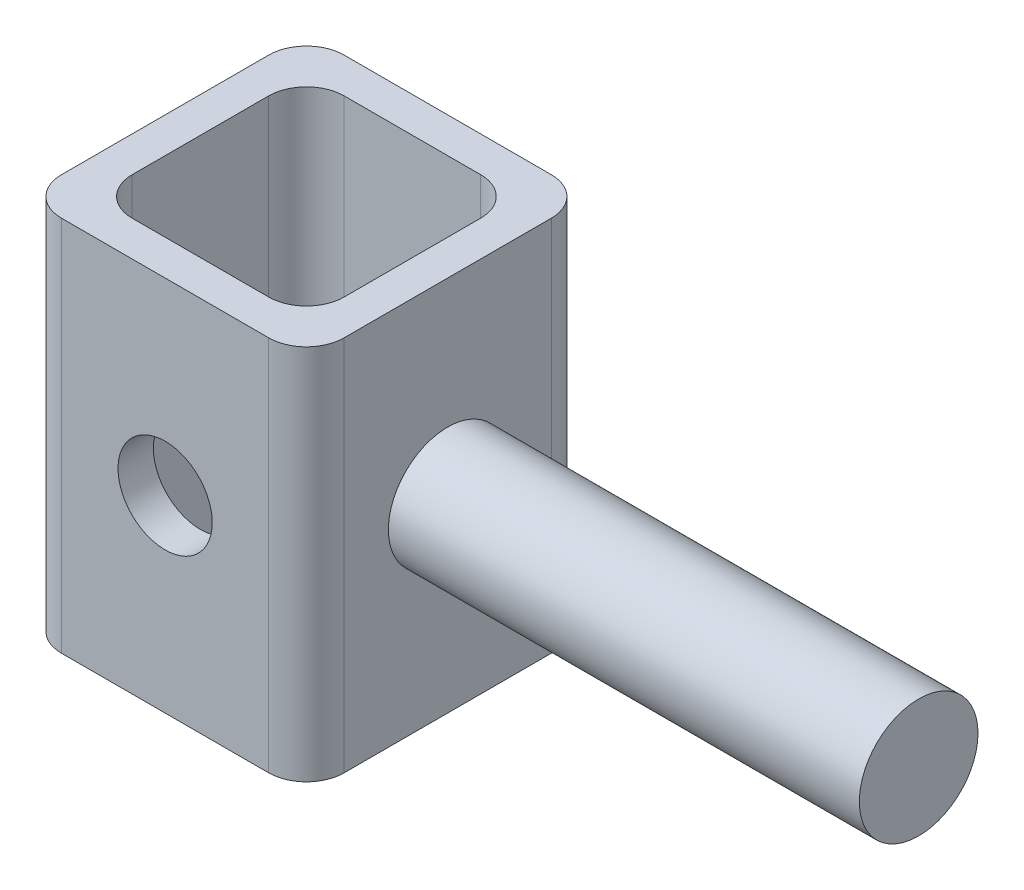
SolidWorks part; units mm, degrees
ref_plane "Front Plane" through (0, 0, 0) normal (0, 0, 1) x (1, 0, 0)
ref_plane "Top Plane" through (0, 0, 0) normal (0, 1, 0) x (1, 0, 0)
ref_plane "Right Plane" through (0, 0, 0) normal (1, 0, 0) x (0, 0, -1)
sketch "Sketch1" plane through (0, 0, 0) normal (0, 1, 0) x (1, 0, 0)
  line L1 (0, 0) -> (19.05, 0)
  line L2 (0, 0) -> (0, 19.05)
  line L3 (0, 19.05) -> (19.05, 19.05)
  line L4 (19.05, 0) -> (19.05, 19.05)
  line L5 (2.3813, 2.3813) -> (16.6687, 2.3813)
  line L6 (2.3813, 2.3813) -> (2.3813, 16.6687)
  line L7 (2.3813, 16.6687) -> (16.6687, 16.6687)
  line L8 (16.6687, 2.3813) -> (16.6687, 16.6687)
  dimension "D1" = 19.05
  dimension "D2" = 2.3813
  dimension "D3" = 2.3813
  dimension "D4" = 2.3813
extrude "Boss-Extrude1" add sketch "Sketch1" along normal blind 25.4
sketch "Sketch2" plane through (0, 0, 0) normal (0, 0, 1) x (1, 0, 0)
  line L0 (0, 25.4) -> (19.05, 25.4) construction
  line L1 (0, 25.4) -> (0, 0) construction
  circle A0 centre (9.525, 12.7) radius 3.175
  point P4 (9.525, 25.4)
  point P7 (0, 12.7)
  dimension "D1" = 6.35
extrude "Cut-Extrude1" cut sketch "Sketch2" against normal up to next
sketch "Sketch3" plane through (19.05, 0, 0) normal (1, 0, 0) x (0, 0, -1)
  line L0 (0, 25.4) -> (19.05, 25.4) construction
  line L1 (0, 25.4) -> (0, 0) construction
  circle A0 centre (9.525, 12.7) radius 4
  point P4 (9.525, 25.4)
  point P7 (0, 12.7)
  dimension "D1" = 8
extrude "Boss-Extrude2" add sketch "Sketch3" along normal blind 31.75
fillet "Fillet1" radius 2.54 8 edges at (16.6687, 12.7, -16.6687) (16.6687, 12.7, -2.3813) (2.3813, 12.7, -2.3813) (2.3813, 12.7, -16.6687) (19.05, 12.7, 0) (0, 12.7, 0) (0, 12.7, -19.05) (19.05, 12.7, -19.05)
